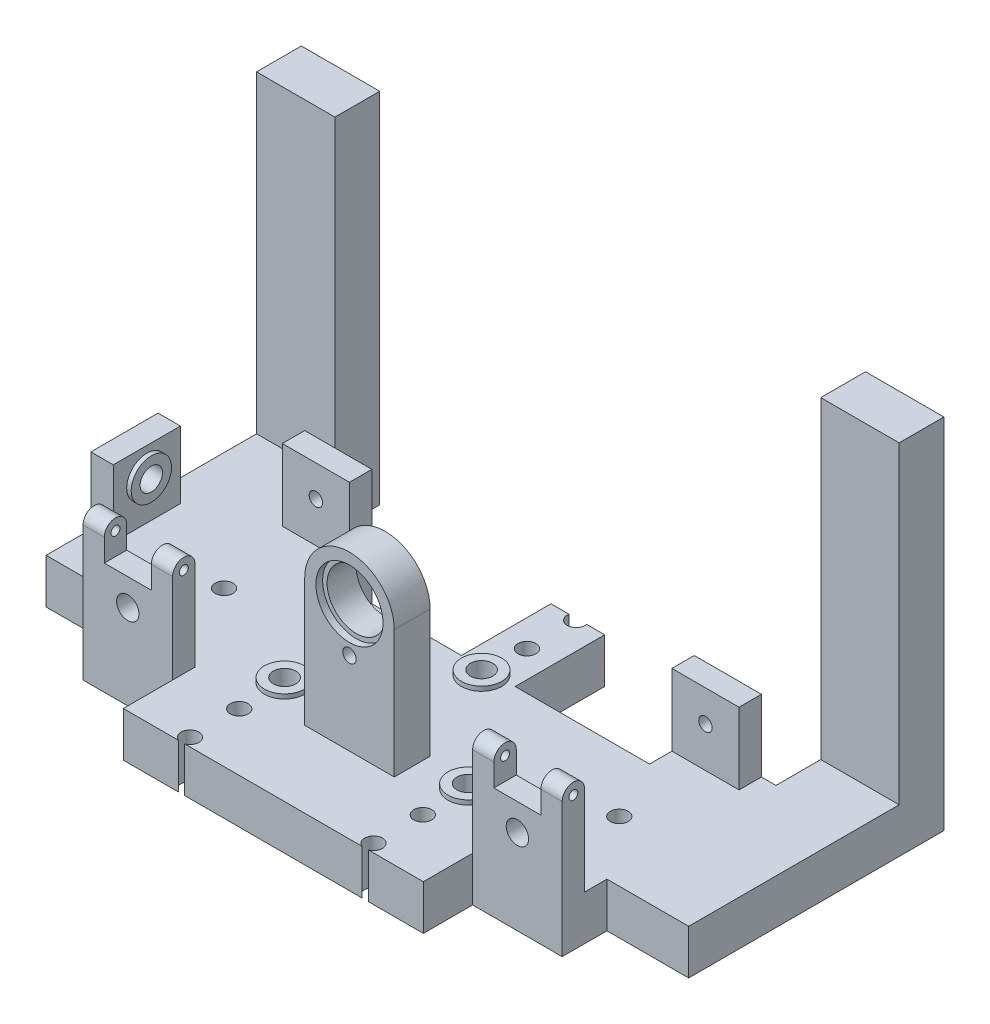
SolidWorks part; units mm, degrees
material "铸造碳钢"
ref_plane "前视基准面" through (0, 0, 0) normal (0, 0, 1) x (1, 0, 0)
ref_plane "上视基准面" through (0, 0, 0) normal (0, 1, 0) x (1, 0, 0)
ref_plane "右视基准面" through (0, 0, 0) normal (1, 0, 0) x (0, 0, -1)
sketch "草图1" plane through (0, 0, 0) normal (0, 1, 0) x (1, 0, 0)
  line L1 (-67, 0) -> (67, 0)
  line L9 (-143.5, 42) -> (-107, 42)
  line L10 (-107, 42) -> (-107, 22)
  line L11 (143.5, 42) -> (107, 42)
  line L12 (107, 42) -> (107, 22)
  line L13 (-107, 22) -> (-67, 22)
  line L14 (-67, 22) -> (-67, 0)
  line L15 (107, 22) -> (67, 22)
  line L16 (67, 22) -> (67, 0)
  line L21 (-72, 116) -> (-72, 96)
  line L22 (-72, 96) -> (-12, 96)
  line L25 (12, 96) -> (72, 96)
  line L26 (72, 96) -> (72, 116)
  line L27 (-12, 136) -> (-12, 96)
  line L28 (-12, 136) -> (12, 136)
  line L29 (12, 136) -> (12, 96)
  line L30 (-72, 116) -> (-143.5, 116)
  line L31 (-143.5, 116) -> (-143.5, 42)
  line L32 (72, 116) -> (143.5, 116)
  line L33 (143.5, 116) -> (143.5, 42)
  point P18 (0, 0)
  dimension "D2" = 60
  dimension "D3" = 71.5
  dimension "D4" = 74
  dimension "D5" = 60
  dimension "D6" = 40
  dimension "D7" = 287
  dimension "D8" = 71.5
  dimension "D9" = 36.5
  dimension "D10" = 76.5
  dimension "D11" = 36.5
  dimension "D12" = 76.5
  dimension "D13" = 22
  dimension "D14" = 42
  dimension "D18" = 20
extrude "凸台-拉伸1" add sketch "草图1" along normal blind 20
sketch "草图3" plane through (0, 20, 0) normal (0, 1, 0) x (1, 0, 0)
  line L0 (-133.5, 92) -> (-133.5, 62)
  line L1 (-133.5, 62) -> (-143.5, 62)
  line L2 (-143.5, 62) -> (-143.5, 92)
  line L3 (-143.5, 92) -> (-133.5, 92)
  line L4 (-67, 0) -> (67, 0) construction
  line L7 (-143.5, 116) -> (-143.5, 42) construction
  dimension "D1" = 30
  dimension "D2" = 10
  dimension "D3" = 62
extrude "凸台-拉伸2" add sketch "草图3" along normal blind 30
sketch "草图5" plane through (0, 20, 0) normal (0, 1, 0) x (1, 0, 0)
  line L0 (-107, 32) -> (-107, 22)
  line L1 (-107, 22) -> (-67, 22)
  line L2 (-67, 22) -> (-67, 32)
  line L3 (-67, 32) -> (-107, 32)
  line L4 (67, 32) -> (67, 22)
  line L5 (67, 22) -> (107, 22)
  line L6 (107, 22) -> (107, 32)
  line L7 (107, 32) -> (67, 32)
  line L8 (-67, 0) -> (67, 0) construction
  line L9 (-133.5, 62) -> (-133.5, 92) construction
  dimension "D1" = 10
  dimension "D2" = 40
  dimension "D3" = 10
  dimension "D4" = 40
  dimension "D5" = 32
  dimension "D6" = 32
  dimension "D7" = 26.5
  dimension "D8" = 134
extrude "凸台-拉伸3" add sketch "草图5" along normal blind 30
sketch "草图2" plane through (0, 20, 0) normal (0, 1, 0) x (1, 0, 0)
  line L0 (132.9483, 93) -> (219.6658, 93) construction
  line L1 (123.0215, 46) -> (237.8074, 46) construction
  line L2 (-41, 68.6858) -> (-41, 50.7818) construction
  line L3 (41, 68.6858) -> (41, 53.2784) construction
  line L4 (0, 122.8842) -> (0, 97.7435) construction
  line L6 (-133.5, 62) -> (-133.5, 92) construction
  line L7 (-67, 32) -> (-107, 32) construction
  circle A1 centre (0, 93) radius 5
  circle A2 centre (-41, 46) radius 5
  circle A3 centre (41, 46) radius 5
  dimension "D1" = 10
  dimension "D2" = 10
  dimension "D3" = 10
  dimension "D4" = 14
  dimension "D5" = 47
  dimension "D6" = 92.5
  dimension "D7" = 82
  dimension "D8" = 133.5
extrude "切除-拉伸1" cut sketch "草图2" against normal blind 13
sketch "草图4" plane through (-133.5, 0, 0) normal (1, 0, 0) x (0, 0, -1)
  line L0 (92, 50) -> (92, 20) construction
  line L1 (62, 20) -> (92, 20) construction
  circle A0 centre (77, 38) radius 5
  dimension "D1" = 10
  dimension "D2" = 15
  dimension "D3" = 18
extrude "切除-拉伸2" cut sketch "草图4" against normal up to next
sketch "草图6" plane through (0, 0, -32) normal (0, 0, -1) x (-1, 0, 0)
  line L0 (67, 20) -> (107, 20) construction
  line L1 (-107, 20) -> (-67, 20) construction
  line L2 (67, 50) -> (67, 20) construction
  line L3 (-67, 50) -> (-67, 20) construction
  circle A0 centre (87, 38) radius 5
  circle A1 centre (-87, 38) radius 5
  dimension "D1" = 10
  dimension "D2" = 10
  dimension "D3" = 18
  dimension "D4" = 18
  dimension "D5" = 20
  dimension "D6" = 20
extrude "切除-拉伸3" cut sketch "草图6" against normal up to next
sketch "草图7" plane through (-133.5, 0, 0) normal (1, 0, 0) x (0, 0, -1)
  circle A0 centre (77, 38) radius 9
  circle A1 centre (77, 38) radius 5 construction
  circle A2 centre (77, 38) radius 5
  dimension "D1" = 18
extrude "凸台-拉伸4" add sketch "草图7" along normal blind 2
sketch "草图8" plane through (0, 0, -32) normal (0, 0, -1) x (-1, 0, 0)
  circle A0 centre (87, 38) radius 5 construction
  circle A1 centre (-87, 38) radius 5 construction
  circle A2 centre (87, 38) radius 5
  circle A3 centre (-87, 38) radius 5
  circle A4 centre (-87, 38) radius 9
  circle A5 centre (87, 38) radius 9
  dimension "D1" = 18
  dimension "D2" = 18
extrude "凸台-拉伸5" add sketch "草图8" along normal blind 2
sketch "草图9" plane through (0, 20, 0) normal (0, 1, 0) x (1, 0, 0)
  circle A0 centre (-41, 46) radius 9
  circle A1 centre (0, 93) radius 9
  circle A2 centre (41, 46) radius 9
  circle A3 centre (-41, 46) radius 5 construction
  circle A4 centre (0, 93) radius 5 construction
  circle A5 centre (41, 46) radius 5 construction
  circle A6 centre (-41, 46) radius 5
  circle A7 centre (0, 93) radius 5
  circle A8 centre (41, 46) radius 5
  dimension "D1" = 18
  dimension "D2" = 18
  dimension "D3" = 18
extrude "凸台-拉伸6" add sketch "草图9" along normal blind 2
sketch "草图11" plane through (0, 20, 0) normal (0, 1, 0) x (1, 0, 0)
  line L0 (-133.5, 62) -> (-133.5, 92) construction
  line L1 (-20, 50) -> (20, 50)
  line L2 (-20, 50) -> (-20, 34)
  line L3 (-20, 34) -> (20, 34)
  line L4 (20, 50) -> (20, 34)
  line L7 (-67, 0) -> (67, 0) construction
  dimension "D1" = 40
  dimension "D2" = 16
  dimension "D3" = 113.5
  dimension "D4" = 34
extrude "凸台-拉伸7" add sketch "草图11" along normal blind 57
sketch "草图12" plane through (0, 77, 0) normal (0, 1, 0) x (1, 0, 0)
  line L5 (0, 34) -> (-20, 34)
  line L6 (-20, 34) -> (20, 34) construction
  line L7 (-20, 34) -> (-20, 50)
  line L8 (-20, 50) -> (0, 50)
  line L9 (20, 50) -> (-20, 50) construction
  line L10 (0, 50) -> (0, 34)
revolve "旋转1" add sketch "草图12" angle 180 about L10
sketch "草图13" plane through (0, 0, -34) normal (0, 0, 1) x (1, 0, 0)
  circle A0 centre (0, 77) radius 15
  arc A1 (20, 77) -> (-20, 77) centre (0, 77) ccw construction
  dimension "D1" = 30
extrude "切除-拉伸5" cut sketch "草图13" against normal blind 3 and the other way through all
sketch "草图14" plane through (0, 0, -37) normal (0, 0, 1) x (1, 0, 0)
  circle A0 centre (0, 77) radius 13
  dimension "D1" = 26
extrude "切除-拉伸6" cut sketch "草图14" against normal up to next
sketch "草图15" plane through (0, 0, -34) normal (0, 0, 1) x (1, 0, 0)
  circle A0 centre (0, 77) radius 20 construction
  circle A1 centre (0, 57) radius 3
  dimension "D1" = 40
  dimension "D2" = 6
extrude "切除-拉伸7" cut sketch "草图15" against normal blind 12
sketch "草图10" plane through (0, 20, 0) normal (0, 1, 0) x (1, 0, 0)
  line L0 (-67, 32) -> (-107, 32) construction
  line L1 (67, 32) -> (67, 22) construction
  line L2 (107, 32) -> (67, 32) construction
  line L3 (-67, 22) -> (-67, 32) construction
  line L4 (0, 93) -> (0, 157.8551) construction
  line L5 (-133.5, 62) -> (-133.5, 92) construction
  line L6 (-67, 32) -> (-107, 32) construction
  line L7 (107, 32) -> (67, 32) construction
  circle A0 centre (-41, 25.75) radius 4
  circle A1 centre (41, 25.75) radius 4
  circle A2 centre (-41, 3.75) radius 4
  circle A3 centre (41, 3.75) radius 4
  circle A6 centre (-91, 69) radius 4
  circle A7 centre (0, 113.25) radius 4
  circle A8 centre (0, 135.25) radius 4
  circle A9 centre (85.5, 69) radius 4
  circle A10 centre (0, 93) radius 5 construction
  dimension "D2" = 8
  dimension "D3" = 8
  dimension "D7" = 8
  dimension "D8" = 8
  dimension "D10" = 22
  dimension "D11" = 20.25
  dimension "D12" = 42.5
  dimension "D13" = 37
  dimension "D14" = 8
  dimension "D15" = 8
  dimension "D18" = 8
  dimension "D19" = 8
  dimension "D1" = 6.25
  dimension "D4" = 6.25
  dimension "D5" = 26
  dimension "D6" = 26
  dimension "D9" = 22
  dimension "D16" = 37
  dimension "D17" = 176.5
extrude "切除-拉伸4" cut sketch "草图10" against normal through all
ref_plane "基准面1" through (0, 50, 0) normal (0, 1, 0) x (1, 0, 0)
sketch "草图16" plane through (107, 0, 0) normal (1, 0, 0) x (0, 0, -1)
  line L4 (22, 50) -> (22, 60)
  line L5 (32, 60) -> (32, 50)
  line L6 (22, 50) -> (32, 50)
  arc A1 (22, 60) -> (32, 60) centre (27, 60) cw
  dimension "D1" = 10
extrude "凸台-拉伸8" add sketch "草图16" against normal blind 40
sketch "草图17" plane through (45, 50, 0) normal (0, -1, 0) x (0, 0, -1)
  line L9 (32, 52.5) -> (22, 52.5)
  line L10 (32, 62) -> (32, 22) construction
  line L11 (22, 22) -> (22, 62) construction
  line L12 (22, 52.5) -> (22, 31.5)
  line L13 (22, 31.5) -> (32, 31.5)
  line L14 (32, 31.5) -> (32, 52.5)
  line L15 (32, 62) -> (22, 62) construction
  line L16 (22, 22) -> (32, 22) construction
  dimension "D1" = 9.5
  dimension "D2" = 9.5
extrude "切除-拉伸8" cut sketch "草图17" against normal up to next (15 mm away)
sketch "草图18" plane through (107, 0, 0) normal (1, 0, 0) x (0, 0, -1)
  circle A0 centre (27, 60) radius 2
  arc A1 (32, 60) -> (22, 60) centre (27, 60) ccw construction
  dimension "D1" = 4
extrude "切除-拉伸9" cut sketch "草图18" along direction (1, 0, 0) on the side against the normal up to surface (40 mm away)
mirror "镜向1" about plane through (0, 0, 0) normal (1, 0, 0) of "切除-拉伸9", "切除-拉伸8", "凸台-拉伸8"
sketch "草图19" plane through (0, 20, 0) normal (0, 1, 0) x (1, 0, 0)
  line L17 (-72, 116) -> (-102, 116)
  line L18 (-72, 116) -> (-72, 106)
  line L19 (-72, 106) -> (-102, 106)
  line L20 (-102, 116) -> (-102, 106)
  line L21 (72, 116) -> (102, 116)
  line L22 (72, 116) -> (72, 106)
  line L23 (72, 106) -> (102, 106)
  line L24 (102, 116) -> (102, 106)
  dimension "D1" = 10
  dimension "D2" = 30
  dimension "D3" = 30
  dimension "D4" = 10
extrude "凸台-拉伸9" add sketch "草图19" along normal blind 32
sketch "草图20" plane through (0, 0, -116) normal (0, 0, -1) x (-1, 0, 0)
  line L4 (-102, 52) -> (-102, 20) construction
  line L5 (-102, 52) -> (-72, 52) construction
  line L7 (72, 52) -> (72, 0) construction
  line L8 (72, 52) -> (102, 52) construction
  circle A0 centre (-87, 38) radius 3
  circle A1 centre (87, 38) radius 3
  dimension "D1" = 6
  dimension "D2" = 6
  dimension "D3" = 15
  dimension "D4" = 14
  dimension "D5" = 14
  dimension "D6" = 15
extrude "切除-拉伸10" cut sketch "草图20" against normal blind 20
sketch "草图21" plane through (0, 0, -116) normal (0, 0, -1) x (-1, 0, 0)
  line L0 (-143.5, 20) -> (-143.5, 0)
  line L1 (-143.5, 0) -> (-108.5, 0)
  line L2 (-143.5, 0) -> (-72, 0) construction
  line L3 (-108.5, 0) -> (-108.5, 20)
  line L4 (-143.5, 20) -> (-102, 20) construction
  line L5 (-108.5, 20) -> (-143.5, 20)
  line L6 (143.5, 20) -> (108.5, 20)
  line L7 (102, 20) -> (143.5, 20) construction
  line L8 (108.5, 20) -> (108.5, 0)
  line L9 (72, 0) -> (143.5, 0) construction
  line L10 (108.5, 0) -> (143.5, 0)
  line L11 (143.5, 0) -> (143.5, 20)
  dimension "D1" = 35
  dimension "D2" = 35
extrude "凸台-拉伸10" add sketch "草图21" along normal blind 40
sketch "草图22" plane through (0, 20, 0) normal (0, 1, 0) x (1, 0, 0)
  line L0 (-143.5, 156) -> (-143.5, 136)
  line L1 (-143.5, 156) -> (-143.5, 92) construction
  line L2 (-143.5, 136) -> (-108.5, 136)
  line L3 (-108.5, 156) -> (-108.5, 116) construction
  line L4 (-108.5, 136) -> (-108.5, 156)
  line L5 (-108.5, 156) -> (-143.5, 156)
  line L6 (108.5, 156) -> (108.5, 136)
  line L7 (108.5, 156) -> (108.5, 116) construction
  line L8 (108.5, 136) -> (143.5, 136)
  line L9 (143.5, 42) -> (143.5, 156) construction
  line L10 (143.5, 136) -> (143.5, 156)
  line L11 (143.5, 156) -> (108.5, 156)
  dimension "D1" = 20
extrude "凸台-拉伸11" add sketch "草图22" along normal blind 140
